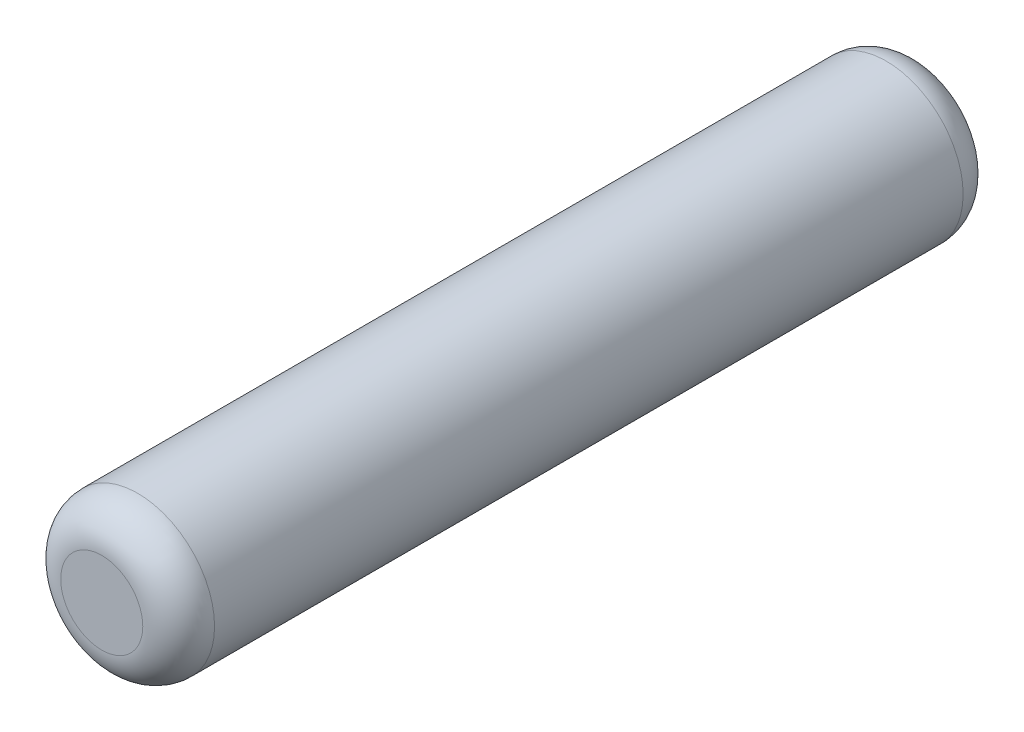
SolidWorks part; units mm, degrees
ref_plane "Front" through (0, 0, 0) normal (0, 0, 1) x (1, 0, 0)
ref_plane "Top" through (0, 0, 0) normal (0, 1, 0) x (1, 0, 0)
ref_plane "Right" through (0, 0, 0) normal (1, 0, 0) x (0, 0, -1)
sketch "Sketch1" plane through (0, 0, 0) normal (0, 0, 1) x (1, 0, 0)
  circle A0 centre (0, 0) radius 0.75
  dimension "D1" = 1.5
extrude "Boss-Extrude1" add sketch "Sketch1" along normal mid plane 8
fillet "Fillet1" radius 0.35 2 edges at (0.75, 0, -4) (0.75, 0, 4)
